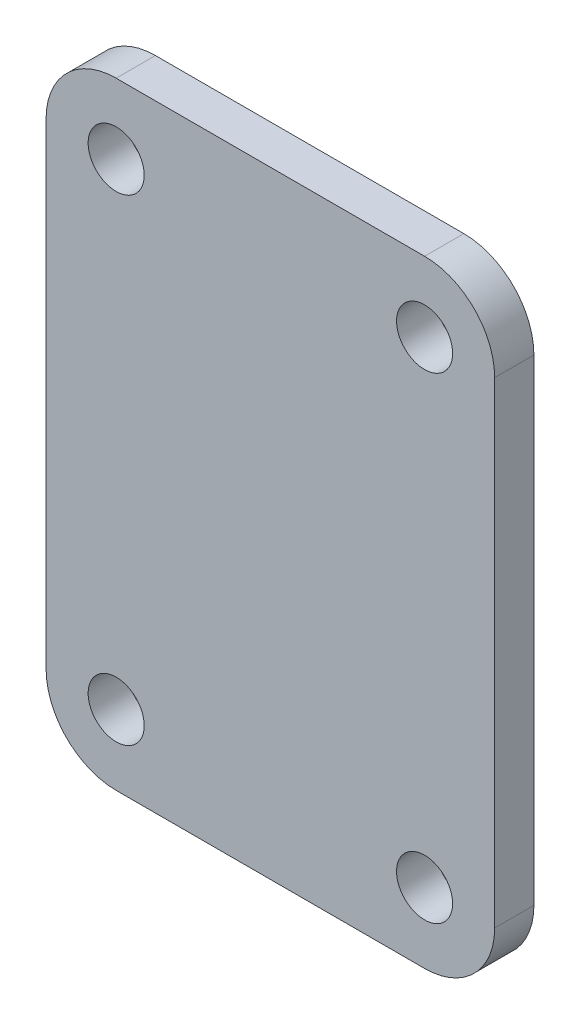
SolidWorks part; units mm, degrees
ref_plane "Plan de face" through (0, 0, 0) normal (0, 0, 1) x (1, 0, 0)
ref_plane "Plan de dessus" through (0, 0, 0) normal (0, 1, 0) x (1, 0, 0)
ref_plane "Plan de droite" through (0, 0, 0) normal (1, 0, 0) x (0, 0, -1)
sketch "Esquisse2" plane through (0, 0, 0) normal (0, 0, 1) x (1, 0, 0)
  line L1 (-621, 210) -> (-566, 210)
  line L2 (-633.5, 197.5) -> (-633.5, 112.5)
  line L3 (-621, 100) -> (-566, 100)
  line L4 (-553.5, 197.5) -> (-553.5, 112.5)
  circle A4 centre (-621, 197.5) radius 5
  circle A5 centre (-566, 197.5) radius 5
  circle A6 centre (-566, 112.5) radius 5
  circle A7 centre (-621, 112.5) radius 5
  arc A8 (-553.5, 197.5) -> (-566, 210) centre (-566, 197.5) ccw
  arc A9 (-566, 100) -> (-553.5, 112.5) centre (-566, 112.5) ccw
  arc A10 (-633.5, 112.5) -> (-621, 100) centre (-621, 112.5) ccw
  arc A11 (-621, 210) -> (-633.5, 197.5) centre (-621, 197.5) ccw
  dimension "D5" = 12.5
  dimension "D1" = 12.5
  dimension "D2" = 12.5
  dimension "D3" = 12.5
  dimension "D4" = 12.5
extrude "Extrusion1" add sketch "Esquisse2" along normal blind 7
